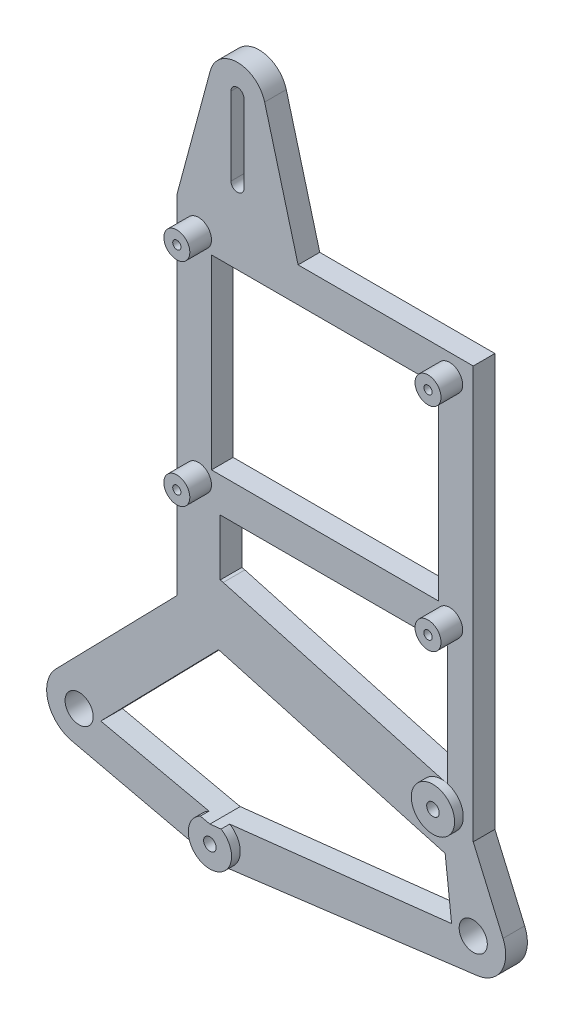
SolidWorks part; units mm, degrees
ref_plane "Front Plane" through (0, 0, 0) normal (0, 0, 1) x (1, 0, 0)
ref_plane "Top Plane" through (0, 0, 0) normal (0, 1, 0) x (1, 0, 0)
ref_plane "Right Plane" through (0, 0, 0) normal (1, 0, 0) x (0, 0, -1)
sketch "Sketch1" plane through (0, 0, 0) normal (0, 0, 1) x (1, 0, 0)
  line L0 (-5.3671, 5.2387) -> (22.56, 33.8503)
  line L1 (33.2733, 41.8533) -> (85, 27.4447)
  line L2 (91, 18.8503) -> (97.8808, 2.984)
  line L3 (91.9464, -7.44) -> (32.831, -14.96)
  line L4 (31.0752, -14.8718) -> (-1.6872, -7.3078)
  line L5 (22.56, 33.8503) -> (22.56, 114)
  line L6 (32.56, 41.9838) -> (32.56, 55)
  line L8 (91, 114) -> (91, 18.8503)
  line L9 (32.56, 55) -> (85, 55)
  line L10 (85, 55) -> (85, 27.4447)
  line L12 (30.56, 63) -> (83, 63)
  line L13 (30.56, 63) -> (30.56, 106)
  line L14 (30.56, 106) -> (83, 106)
  line L15 (83, 63) -> (83, 106)
  line L17 (50.56, 114) -> (42.8365, 142.6897)
  line L18 (22.56, 114) -> (30.2835, 142.6897)
  line L19 (50.56, 114) -> (91, 114)
  line L20 (36.56, 141) -> (36.56, 123) construction
  line L23 (32.2, -6) -> (5, 0)
  line L24 (5, 0) -> (32.2, 27.8667)
  line L26 (86, 0) -> (32.2, -6)
  line L27 (38.06, 141) -> (38.06, 123)
  line L28 (35.06, 141) -> (35.06, 123)
  line L35 (32.2, 27.8667) -> (84.5175, 13.2935)
  line L36 (84.5175, 13.2935) -> (86, 0)
  circle A0 centre (0, 0) radius 3.25
  circle A1 centre (91, 0) radius 3.25
  circle A3 centre (32.2, -10) radius 1.45
  circle A4 centre (83.7, 22.7) radius 1.45
  arc A5 (33.2733, 41.8533) -> (32.56, 41.9838) centre (32.2, 38) ccw
  arc A7 (31.0752, -14.8718) -> (32.831, -14.96) centre (32.2, -10) ccw
  arc A8 (-5.3671, 5.2387) -> (-1.6872, -7.3078) centre (0, 0) ccw
  arc A9 (91.9464, -7.44) -> (97.8808, 2.984) centre (91, 0) ccw
  circle A10 centre (27.56, 109) radius 0.95
  circle A11 centre (27.56, 60) radius 0.95
  circle A12 centre (85.56, 60) radius 0.95
  circle A13 centre (85.56, 109) radius 0.95
  arc A14 (42.8365, 142.6897) -> (30.2835, 142.6897) centre (36.56, 141) ccw
  arc A15 (38.06, 141) -> (35.06, 141) centre (36.56, 141) ccw
  arc A16 (35.06, 123) -> (38.06, 123) centre (36.56, 123) ccw
  point P7 (0, 0)
  point P29 (0, 0)
  point P40 (36.56, 132)
  point P49 (0, 0)
  dimension "D1" = 6.5
  dimension "D2" = 6.5
  dimension "D7" = 2.9
  dimension "D8" = 4
  dimension "D9" = 2.9
  dimension "D12" = 7.5
  dimension "D13" = 7.5
  dimension "D14" = 15
  dimension "D15" = 5
  dimension "D16" = 4
  dimension "D27" = 1.9
  dimension "D28" = 1.9
  dimension "D29" = 1.9
  dimension "D30" = 1.9
  dimension "D38" = 13
  dimension "D40" = 18
  dimension "D37" = 14
  dimension "D39" = 1.5
  dimension "D3" = 91
  dimension "D4" = 48
  dimension "D5" = 32.2
  dimension "D6" = 10
  dimension "D10" = 15.3
  dimension "D11" = 51.5
  dimension "D17" = 10
  dimension "D18" = 6
  dimension "D19" = 52.44
  dimension "D20" = 22.56
  dimension "D21" = 17
  dimension "D22" = 8
  dimension "D23" = 8
  dimension "D24" = 8
  dimension "D25" = 8
  dimension "D26" = 43
  dimension "D31" = 49
  dimension "D32" = 58
  dimension "D33" = 3
  dimension "D34" = 60
  dimension "D35" = 28
  dimension "D36" = 27
  dimension "D41" = 8.5943
  dimension "D42" = 5
  dimension "D43" = 5
extrude "Boss-Extrude1" add sketch "Sketch1" along normal blind 5
sketch "Sketch2" plane through (0, 0, 5) normal (0, 0, 1) x (1, 0, 0)
  line L0 (32.2, -6) -> (34.7733, -5.713)
  line L1 (32.2, -6) -> (86, 0) construction
  line L2 (32.2, -6) -> (29.9934, -5.5133)
  line L3 (5, 0) -> (32.2, -6) construction
  circle A0 centre (32.2, -10) radius 1.45
  arc A1 (29.9934, -5.5133) -> (34.7733, -5.713) centre (32.2, -10) ccw
  circle A2 centre (83.7, 22.7) radius 1.45
  circle A3 centre (83.7, 22.7) radius 5
  circle A4 centre (32.2, -10) radius 1.45 construction
  circle A5 centre (83.7, 22.7) radius 1.45 construction
  dimension "D1" = 10
  dimension "D2" = 10
extrude "Boss-Extrude2" add sketch "Sketch2" along normal blind 2
sketch "Sketch3" plane through (0, 0, 5) normal (0, 0, 1) x (1, 0, 0)
  circle A0 centre (27.56, 60) radius 0.9456
  circle A1 centre (27.56, 60) radius 3
  circle A2 centre (85.56, 60) radius 0.9765
  circle A3 centre (85.56, 60) radius 3
  circle A4 centre (85.56, 109) radius 0.9395
  circle A5 centre (85.56, 109) radius 3
  circle A6 centre (27.56, 109) radius 0.95
  circle A7 centre (27.56, 109) radius 3
  dimension "D1" = 6
  dimension "D2" = 6
  dimension "D3" = 6
  dimension "D4" = 6
extrude "Boss-Extrude3" add sketch "Sketch3" along normal blind 5
